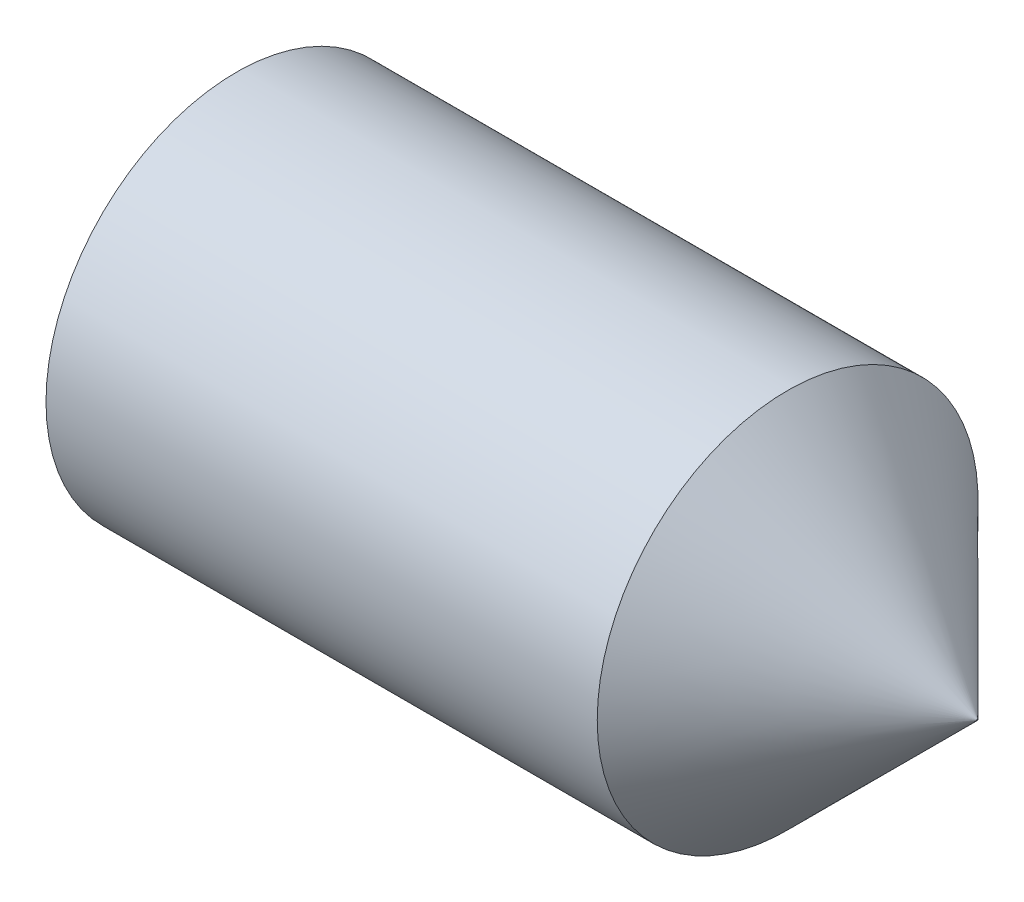
SolidWorks part; units mm, degrees
revolve "BaseBody" add sketch "BodySke" angle 360 about L5
sketch "BodySke" plane through (0, 0, 0) normal (0, 0, 1) x (1, 0, 0)
  line L0 (0, 0) -> (0, 1.2195)
  line L1 (0, 1.2195) -> (0.1619, 1.5)
  line L2 (0.1619, 1.5) -> (4.505, 1.5)
  line L3 (4.505, 1.5) -> (6, 0.005)
  line L4 (6, 0) -> (0, 0)
  line L5 (-12.7, 0) -> (88.9, 0) construction
  line L6 (6, 0.005) -> (6, 0)
  line L7 (6, 0.005) -> (6, 9.53) construction
  line L8 (0, -1.2195) -> (0.1619, -1.5) construction
  line L9 (0.5, 15.875) -> (0.5, -3.175) construction
  line L10 (4.505, -1.5) -> (6, -0.005) construction
  dimension "Diameter" = 3
  dimension "Drive_ch_ang" = 60
  dimension "Minor_dia" = 2.439
  dimension "Tip_dia" = 0.01
  dimension "Length" = 6
  dimension "Advance" = 0.5
  dimension "Cone_ang" = 90
cosmetic thread "ThreadCosmetic" [suppressed] parameters "Thread_minor"=2.439
ref_plane "Plane1" through (0, 0, 0) normal (0, 0, 1) x (1, 0, 0)
ref_plane "Plane2" through (0, 0, 0) normal (0, 1, 0) x (1, 0, 0)
ref_plane "Plane3" through (0, 0, 0) normal (1, 0, 0) x (0, 0, -1)
sketch "Sketch2" plane through (0, 0, 0) normal (-1, 0, 0) x (0, 0, 1)
  line L0 (0.433, 0.75) -> (-0.433, 0.75)
  line L1 (-0.433, 0.75) -> (-0.866, 0)
  line L2 (0.433, 0.75) -> (0.866, 0)
  line L3 (0.433, -0.75) -> (0.866, 0)
  line L4 (0.433, -0.75) -> (-0.433, -0.75)
  line L5 (-0.433, -0.75) -> (-0.866, 0)
  dimension "Hex_size" = 1.5
  dimension "D2" = 0.75
  dimension "D3" = 0.75
extrude "Hex" cut sketch "Sketch2" against normal blind 2
sketch "ThdSchSke" [suppressed] plane through (0, 0, 0) normal (0, 0, 1) x (1, 0, 0)
  line L0 (0.9515, -10.352) -> (-0.2025, -12)
  line L1 (0.9515, -10.352) -> (2.1054, -12)
  line L2 (2.1054, -12) -> (2.1054, -15)
  line L3 (-3.175, 0) -> (5.1513, 0) construction
  line L5 (2.1054, -15) -> (-0.2025, -15)
  line L6 (-0.2025, -15) -> (-0.2025, -12)
  line L8 (0.9515, 12) -> (0.9515, -12) construction
  dimension "Thread_minor" = 2.439
  dimension "Diameter" = 3
revolve "ThreadSchematic" [suppressed] cut sketch "ThdSchSke" angle 360 about L3
pattern_linear "ThdSchPat" [suppressed]
equation "\"D2@Sketch2\" = \"Hex_size@Sketch2\" / 2"
equation "\"D3@Sketch2\" = \"Hex_size@Sketch2\" / 2"
equation "\"Thread_minor@ThreadCosmetic\" = \"Minor_dia@BodySke\""
equation "\"Thread_minor@ThdSchSke\" = \"Thread_minor@ThreadCosmetic\""
equation "\"Diameter@ThdSchSke\" = \"Diameter@BodySke\""
equation "\"Overcut@ThdSchSke\" = \"Diameter@BodySke\" * 1.25"
equation "\"Num_threads@ThdSchPat\" = int( (\"Length@BodySke\" - ( ( ( \"Diameter@BodySke\" - \"Minor_dia@BodySke\" ) * 0.5 ) / tan( \"Drive_ch_ang@BodySke\" * 0.017453292 ) ) - ( ( ( \"Diameter@BodySke\" - \"Tip_dia@BodySke\" ) * 0.5 ) / tan( \"Cone_ang@BodySke\" / 2.0 * 0.017453292 ) ) ) / \"Advance@BodySke\" + 0.999 )  + 1"
equation "\"Advance@ThdSchPat\" = (\"Length@BodySke\" - ( ( ( \"Diameter@BodySke\" - \"Minor_dia@BodySke\" ) * 0.5 ) / tan( \"Drive_ch_ang@BodySke\" * 0.017453292 ) ) - ( ( ( \"Diameter@BodySke\" - \"Tip_dia@BodySke\" ) * 0.5 ) / tan( \"Cone_ang@BodySke\" / 2.0 * 0.017453292 ) ) ) /  (\"Num_threads@ThdSchPat\" - 1) 'relax it"
equation "' \"Num_threads@ThdSchPat\" = \"Num_threads@ThdSchPat\" - sgn( \"Num_threads@ThdSchPat\" - 1) '---chamfered tips only---"
